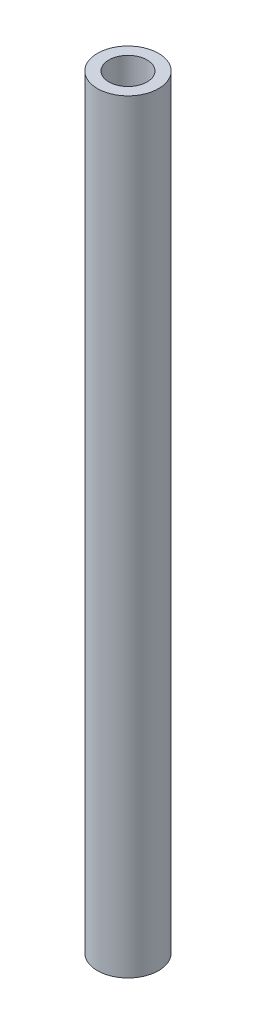
SolidWorks part; units mm, degrees
ref_plane "Front Plane" through (0, 0, 0) normal (0, 0, 1) x (1, 0, 0)
ref_plane "Top Plane" through (0, 0, 0) normal (0, 1, 0) x (1, 0, 0)
ref_plane "Right Plane" through (0, 0, 0) normal (1, 0, 0) x (0, 0, -1)
sketch "Sketch1" plane through (0, 0, 0) normal (0, 1, 0) x (1, 0, 0)
  circle A0 centre (0, 0) radius 5.08
  dimension "D1" = 10.16
extrude "Boss-Extrude1" add sketch "Sketch1" along normal blind 127
sketch "Sketch2" plane through (0, 0, 0) normal (0, -1, 0) x (1, 0, 0)
  circle A0 centre (0, 0) radius 3.175
  dimension "D1" = 6.35
extrude "Cut-Extrude1" cut sketch "Sketch2" against normal through all
